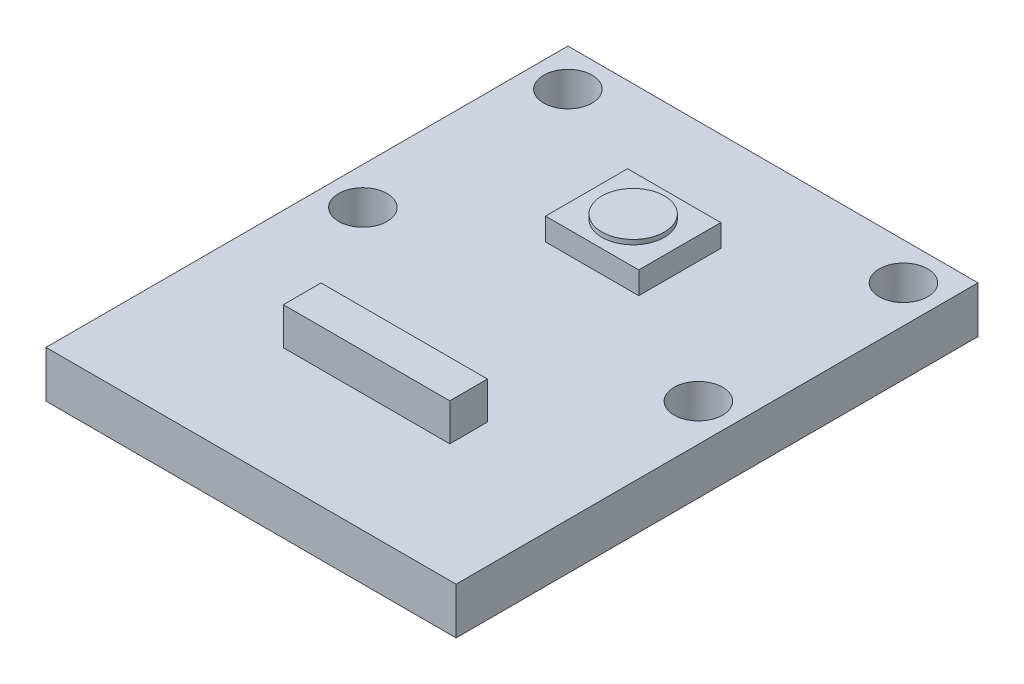
SolidWorks part; units mm, degrees
ref_plane "Front Plane" through (0, 0, 0) normal (0, 0, 1) x (1, 0, 0)
ref_plane "Top Plane" through (0, 0, 0) normal (0, 1, 0) x (1, 0, 0)
ref_plane "Right Plane" through (0, 0, 0) normal (1, 0, 0) x (0, 0, -1)
sketch "Sketch1" plane through (0, 0, 0) normal (0, 1, 0) x (1, 0, 0)
  line L1 (-11, -7.5) -> (11, -7.5)
  line L2 (-11, -7.5) -> (-11, 7.5)
  line L3 (-11, 7.5) -> (11, 7.5)
  line L4 (11, -7.5) -> (11, 7.5)
  line L5 (-11, -7.5) -> (11, 7.5) construction
  line L6 (-11, 7.5) -> (11, -7.5) construction
  point P0 (0, 0)
  dimension "D1" = 22
  dimension "D2" = 15
extrude "Boss-Extrude1" add sketch "Sketch1" along normal blind 2.5
hole_wizard "Ø1.0mm Dowel Hole1" positions "Sketch2" profile "Sketch3" hole size "Ø1.0" standard "ANSI Metric"
sketch "Sketch2" plane through (0, 2.5, 0) normal (0, 1, 0) x (1, 0, 0)
  line L0 (-9, 5.5) -> (9, 5.5) construction
  line L1 (9, 5.5) -> (9, -5.5) construction
  line L2 (9, -5.5) -> (-9, -5.5) construction
  line L3 (-9, -5.5) -> (-9, 5.5) construction
  point P0 (-9, 5.5)
  point P2 (9, 5.5)
  point P4 (9, -5.5)
  point P6 (-9, -5.5)
  point P18 (-9, 0)
  point P20 (0, 5.5)
  dimension "D1" = 11
  dimension "D2" = 18
sketch "Sketch3" plane through (-9, 2.5, -5.5) normal (1, 0, 0) x (0, 0, 1)
  line L0 (0, 0) -> (0, 7.1311)
  line L1 (0, 7.1311) -> (1.3, 6.35)
  line L2 (1.3, 6.35) -> (1.3, 0)
  line L5 (1.3, 0) -> (0, 0)
  line L10 (0, 7.1311) -> (-1.3, 6.35) construction
  line L11 (0, -6.35) -> (0, 107.95) construction
  dimension "Hole Dia." = 2.6
  dimension "Hole Depth" = 6.35
  dimension "Drill Angle" = 118
sketch "Sketch4" plane through (0, 2.5, 0) normal (0, 1, 0) x (1, 0, 0)
  line L1 (-2.5, -2.2) -> (2.5, -2.2)
  line L2 (-2.5, -2.2) -> (-2.5, 2.2)
  line L3 (-2.5, 2.2) -> (2.5, 2.2)
  line L4 (2.5, -2.2) -> (2.5, 2.2)
  line L5 (-2.5, -2.2) -> (2.5, 2.2) construction
  line L6 (-2.5, 2.2) -> (2.5, -2.2) construction
  point P0 (0, 0)
  dimension "D1" = 5
  dimension "D2" = 4.4
extrude "Boss-Extrude2" add sketch "Sketch4" along normal blind 1.2
sketch "Sketch5" plane through (0, 2.5, 0) normal (0, 1, 0) x (1, 0, 0)
  line L0 (11, -7.5) -> (11, 7.5) construction
  line L1 (-11, -7.5) -> (11, -7.5)
  line L2 (-11, -7.5) -> (-11, -20.5)
  line L3 (-11, -20.5) -> (11, -20.5)
  line L4 (11, -7.5) -> (11, -20.5)
  dimension "D1" = 13
extrude "Boss-Extrude3" add sketch "Sketch5" against normal up to surface (2.5 mm away) up to face at (-9, 0, -6.8)
sketch "Sketch6" plane through (0, 2.5, 0) normal (0, 1, 0) x (1, 0, 0)
  line L1 (-4.617, -12.1282) -> (4.3118, -12.1282)
  line L2 (-4.617, -12.1282) -> (-4.617, -14.1506)
  line L3 (-4.617, -14.1506) -> (4.3118, -14.1506)
  line L4 (4.3118, -12.1282) -> (4.3118, -14.1506)
extrude "Boss-Extrude4" add sketch "Sketch6" along normal blind 2
sketch "Sketch7" plane through (0, 3.7, 0) normal (0, 1, 0) x (1, 0, 0)
  circle A0 centre (0, 0) radius 1.6776
extrude "Boss-Extrude5" add sketch "Sketch7" along normal blind 0.25
